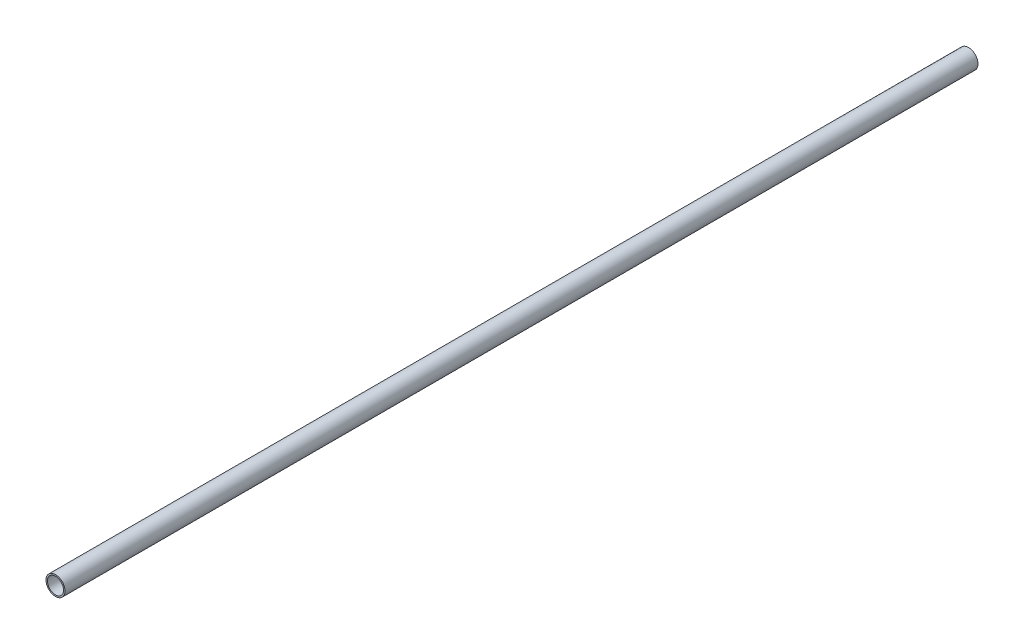
SolidWorks part; units mm, degrees
ref_plane "Front" through (0, 0, 0) normal (0, 0, 1) x (1, 0, 0)
ref_plane "Top" through (0, 0, 0) normal (0, 1, 0) x (1, 0, 0)
ref_plane "Side" through (0, 0, 0) normal (1, 0, 0) x (0, 0, -1)
sketch "PipeSketch" plane through (0, 0, 0) normal (0, 0, 1) x (1, 0, 0)
  circle A0 centre (0, 0) radius 57.15
  circle A1 centre (0, 0) radius 48.5902
  dimension "OuterDiameter" = 114.3
  dimension "InnerDiameter" = 97.1804
extrude "Extrusion" add sketch "PipeSketch" along normal blind 5486.4
sketch "FilterSketch" plane through (0, 0, 0) normal (0, 0, 1) x (1, 0, 0)
  circle A0 centre (0, 0) radius 50.8 construction
  dimension "NominalDiameter" = 101.6
